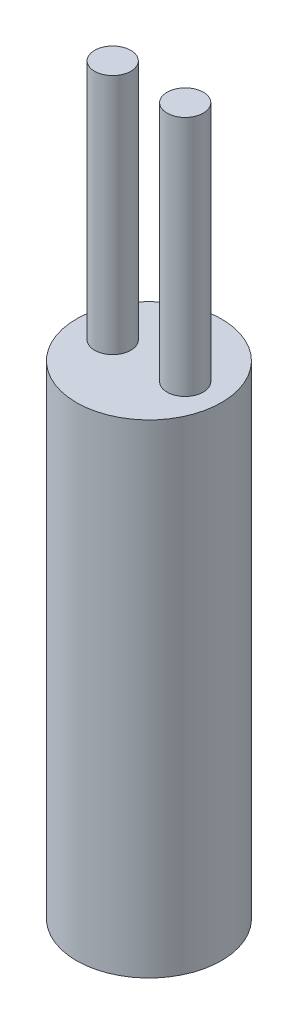
SolidWorks part; units mm, degrees
ref_plane "Front Plane" through (0, 0, 0) normal (0, 0, 1) x (1, 0, 0)
ref_plane "Top Plane" through (0, 0, 0) normal (0, 1, 0) x (1, 0, 0)
ref_plane "Right Plane" through (0, 0, 0) normal (1, 0, 0) x (0, 0, -1)
sketch "Sketch1" plane through (0, 0, 0) normal (0, 1, 0) x (1, 0, 0)
  circle A0 centre (0, 0) radius 3
  dimension "D1" = 6
extrude "Boss-Extrude1" add sketch "Sketch1" along normal blind 20
sketch "Sketch2" plane through (0, 20, 0) normal (0, 1, 0) x (1, 0, 0)
  line L0 (0, -3) -> (0, 3) construction
  circle A0 centre (1.5, 0) radius 0.75
  circle A1 centre (0, 0) radius 3 construction
  circle A2 centre (-1.5, 0) radius 0.75
  dimension "D1" = 1.5
  dimension "D2" = 3
extrude "Boss-Extrude2" add sketch "Sketch2" along normal blind 10
